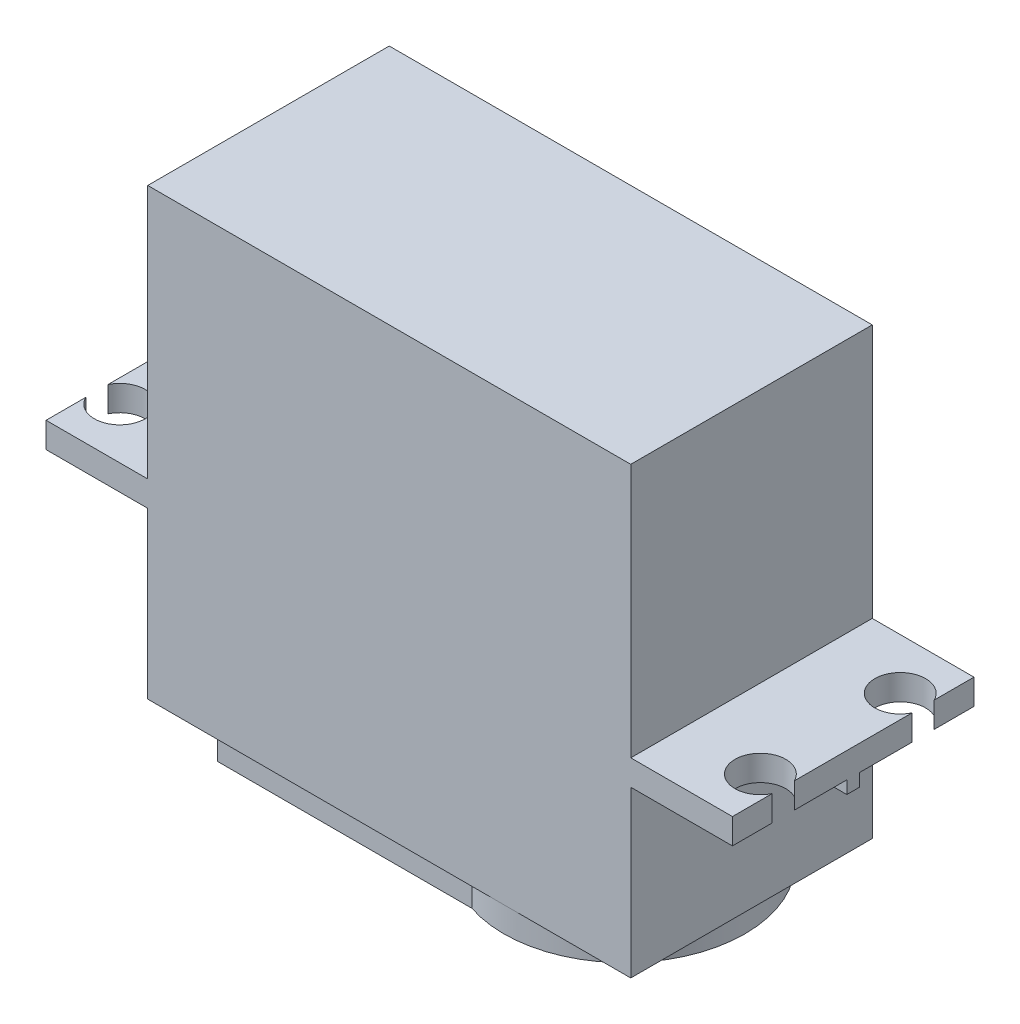
SolidWorks part; units mm, degrees
ref_plane "Front Plane" through (0, 0, 0) normal (0, 0, 1) x (1, 0, 0)
ref_plane "Top Plane" through (0, 0, 0) normal (0, 1, 0) x (1, 0, 0)
ref_plane "Right Plane" through (0, 0, 0) normal (1, 0, 0) x (0, 0, -1)
sketch "Sketch1" plane through (0, 0, 0) normal (0, 0, 1) x (1, 0, 0)
  line L0 (0, 0) -> (0, 37.699) construction
  line L1 (0, 0) -> (48.4915, 0) construction
  line L2 (19, 0) -> (-19, 0)
  line L3 (-19, 0) -> (-19, 13)
  line L4 (-19, 13) -> (-27, 13)
  line L5 (-27, 13) -> (-27, 15)
  line L6 (-27, 15) -> (-19, 15)
  line L7 (-19, 15) -> (-19, 35)
  line L8 (-19, 35) -> (19, 35)
  line L9 (19, 15) -> (19, 35)
  line L10 (27, 15) -> (19, 15)
  line L11 (27, 13) -> (27, 15)
  line L12 (19, 13) -> (27, 13)
  line L13 (19, 0) -> (19, 13)
  point P13 (0, 35)
  dimension "D1" = 19
  dimension "D2" = 13
  dimension "D3" = 2
  dimension "D4" = 35
  dimension "D5" = 8
extrude "Boss-Extrude1" add sketch "Sketch1" along normal blind 19
sketch "Sketch6" plane through (0, 15, 0) normal (0, 1, 0) x (1, 0, 0)
  line L0 (27, -19) -> (27, 0) construction
  line L1 (27, -19) -> (19, -19) construction
  line L2 (19, -9.5) -> (33.7393, -9.5) construction
  line L3 (19, -19) -> (19, 0) construction
  line L4 (0, -19.495) -> (0, 7.5047) construction
  circle A0 centre (25.2, -15) radius 2
  circle A1 centre (25.2, -4) radius 2
  circle A2 centre (-25.2, -4) radius 2
  circle A3 centre (-25.2, -15) radius 2
  dimension "D1" = 4
  dimension "D2" = 1.8
  dimension "D3" = 4
extrude "Cut-Extrude2" cut sketch "Sketch6" against normal through all
sketch "Sketch10" plane through (0, 13, 0) normal (0, -1, 0) x (1, 0, 0)
  line L0 (-19, 9.5) -> (-33.0939, 9.5) construction
  line L1 (-19, 19) -> (-19, 0) construction
  line L2 (-19, 10) -> (-19, 9)
  line L3 (-19, 19) -> (-19, 0) construction
  line L4 (-19, 9) -> (-27, 9)
  line L5 (-27, 14.1282) -> (-27, 4.8718) construction
  line L6 (-27, 9) -> (-27, 10)
  line L7 (-19, 10) -> (-27, 10)
  line L8 (0, 0) -> (0, 26.7518) construction
  line L9 (19, 9.5) -> (33.0939, 9.5) construction
  line L10 (19, 10) -> (27, 10)
  line L11 (27, 9) -> (27, 10)
  line L12 (19, 9) -> (27, 9)
  line L13 (19, 10) -> (19, 9)
  point P12 (-27, 9.5)
  point P22 (27, 9.5)
  dimension "D1" = 0.5
extrude "Boss-Extrude14" add sketch "Sketch10" along normal blind 1
sketch "Sketch12" plane through (0, 0, 0) normal (0, -1, 0) x (1, 0, 0)
  line L0 (-19, 19) -> (-19, 0) construction
  line L1 (-14, 18.5) -> (6, 18.5)
  line L2 (-14, 18.5) -> (-14, 0.5)
  line L3 (-14, 0.5) -> (6, 0.5)
  line L4 (19, 19) -> (19, 10) construction
  line L5 (-19, 19) -> (19, 19) construction
  line L6 (-19, 0) -> (19, 0) construction
  arc A0 (6, 18.5) -> (6, 0.5) centre (9, 9.5) cw
  dimension "D5" = 20
  dimension "D4" = 10
  dimension "D1" = 5
  dimension "D2" = 0.5
  dimension "D3" = 0.5
extrude "Boss-Extrude15" add sketch "Sketch12" along normal blind 2
sketch "Sketch13" plane through (0, -2, 0) normal (0, -1, 0) x (1, 0, 0)
  circle A0 centre (9, 9.5) radius 3
  dimension "D1" = 6
extrude "Cut-Extrude3" cut sketch "Sketch13" against normal blind 5
